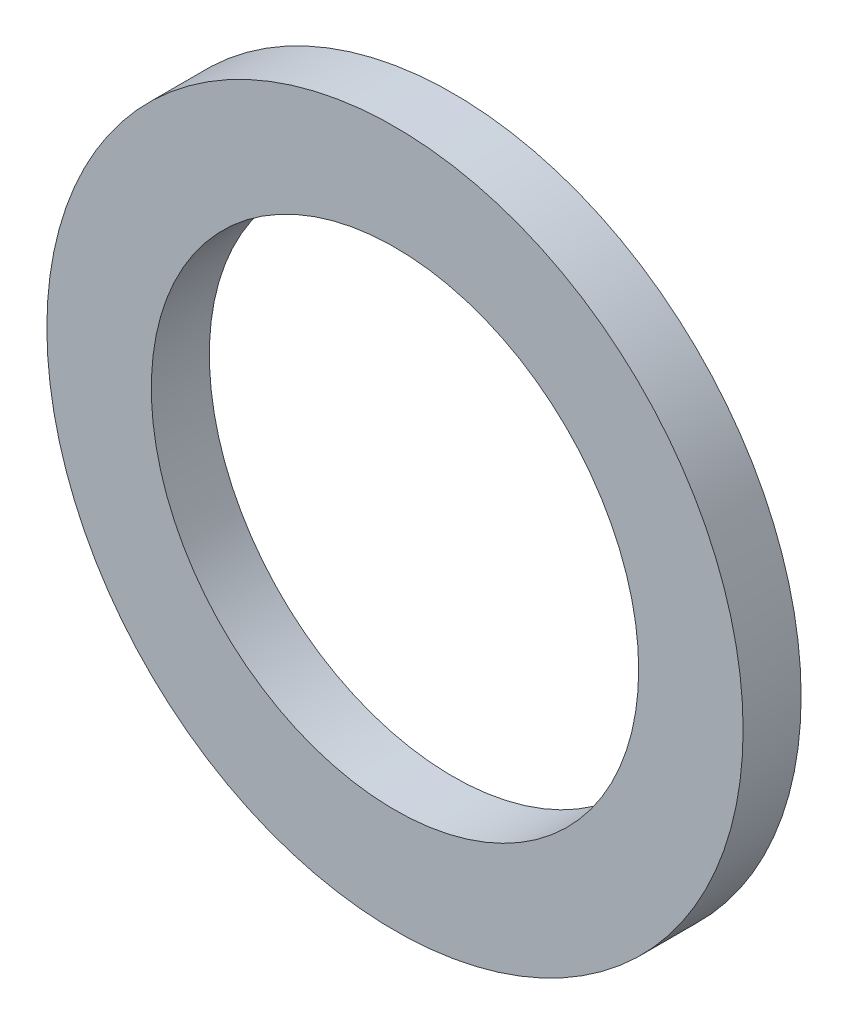
SolidWorks part; units mm, degrees
ref_plane "Plan de face" through (0, 0, 0) normal (0, 0, 1) x (1, 0, 0)
ref_plane "Plan de dessus" through (0, 0, 0) normal (0, 1, 0) x (1, 0, 0)
ref_plane "Plan de droite" through (0, 0, 0) normal (1, 0, 0) x (0, 0, -1)
sketch "Esquisse1" plane through (0, 0, 0) normal (0, 0, 1) x (1, 0, 0)
  circle A0 centre (0, 0) radius 4.2
  circle A1 centre (0, 0) radius 6
  dimension "D1" = 8.4
  dimension "D2" = 12
extrude "Extrusion1" add sketch "Esquisse1" along normal mid plane 1
